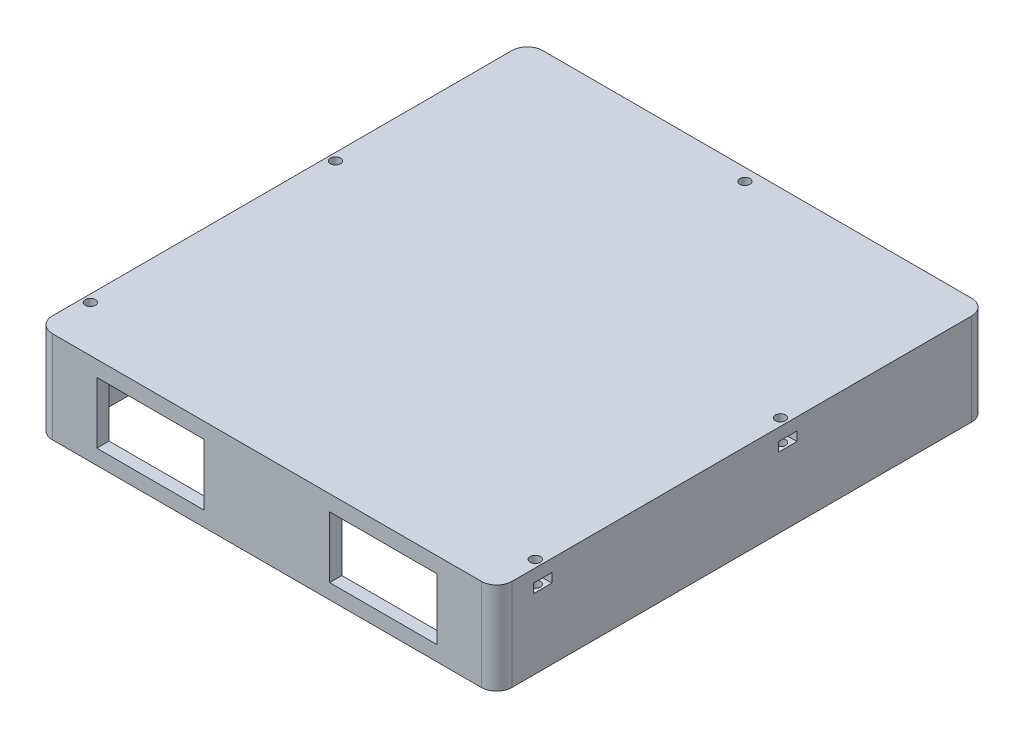
SolidWorks part; units mm, degrees
ref_plane "前视基准面" through (0, 0, 0) normal (0, 0, 1) x (1, 0, 0)
ref_plane "上视基准面" through (0, 0, 0) normal (0, 1, 0) x (1, 0, 0)
ref_plane "右视基准面" through (0, 0, 0) normal (1, 0, 0) x (0, 0, -1)
sketch "草图1" plane through (0, 0, 0) normal (0, 1, 0) x (1, 0, 0)
  line L1 (-75, 80) -> (75, 80)
  line L2 (-75, 80) -> (-75, -80)
  line L3 (-75, -80) -> (75, -80)
  line L4 (75, 80) -> (75, -80)
  line L5 (-75, 80) -> (75, -80) construction
  line L6 (-75, -80) -> (75, 80) construction
  point P0 (0, 0)
  dimension "D1" = 150
  dimension "D2" = 160
extrude "凸台-拉伸1" add sketch "草图1" along normal blind 30
fillet "圆角1" radius 5 4 edges at (75, 15, -80) (-75, 15, -80) (75, 15, 80) (-75, 15, 80)
sketch "草图3" plane through (0, 0, 0) normal (0, -1, 0) x (1, 0, 0)
  line L0 (-70, 80) -> (70, 80) construction
  line L1 (70, 76) -> (-70, 76)
  line L2 (70, 76) -> (70, -76)
  line L3 (70, -76) -> (-70, -76)
  line L4 (-70, 76) -> (-70, -76)
  line L5 (70, 76) -> (-70, -76) construction
  line L6 (70, -76) -> (-70, 76) construction
  line L7 (75, 75) -> (75, -75) construction
  point P0 (0, 0)
  dimension "D1" = 4
  dimension "D2" = 5
extrude "切除-拉伸2" cut sketch "草图3" against normal blind 26
sketch "草图9" plane through (-75, 0, 0) normal (-1, 0, 0) x (0, 0, 1)
  line L0 (80, 30) -> (80, 0) construction
  line L1 (68, 23) -> (62, 23)
  line L2 (68, 23) -> (68, 26)
  line L3 (68, 26) -> (62, 26)
  line L4 (62, 23) -> (62, 26)
  line L5 (68, 23) -> (62, 26) construction
  line L6 (68, 26) -> (62, 23) construction
  line L7 (-75, 30) -> (75, 30) construction
  line L8 (-12, 23) -> (-18, 23)
  line L9 (-12, 23) -> (-12, 26)
  line L10 (-12, 26) -> (-18, 26)
  line L11 (-18, 23) -> (-18, 26)
  line L12 (-12, 23) -> (-18, 26) construction
  line L13 (-12, 26) -> (-18, 23) construction
  point P0 (65, 24.5)
  point P9 (-15, 24.5)
  dimension "D1" = 15
  dimension "D2" = 6
  dimension "D3" = 3
  dimension "D4" = 4
  dimension "D5" = 6
  dimension "D6" = 3
  dimension "D7" = 80
  dimension "D8" = 4
extrude "切除-拉伸7" cut sketch "草图9" against normal through all
fillet "圆角2" radius 2 4 edges at (70, 13, 76) (70, 13, -76) (-70, 13, -76) (-70, 13, 76)
sketch "草图11" plane through (0, 30, 0) normal (0, 1, 0) x (1, 0, 0)
  line L0 (70, 80) -> (-70, 80) construction
  circle A0 centre (0, 76) radius 1.65
  dimension "D1" = 3.3
  dimension "D2" = 4
extrude "切除-拉伸8" cut sketch "草图11" against normal blind 8
sketch "草图12" plane through (0, 0, -80) normal (0, 0, -1) x (-1, 0, 0)
  line L0 (0, 0) -> (0, 95.539) construction
  line L1 (-70, 30) -> (70, 30) construction
  line L2 (3.25, 21.7) -> (-3.25, 21.7)
  line L3 (3.25, 21.7) -> (3.25, 25)
  line L4 (3.25, 25) -> (-3.25, 25)
  line L5 (-3.25, 21.7) -> (-3.25, 25)
  line L6 (3.25, 21.7) -> (-3.25, 25) construction
  line L7 (3.25, 25) -> (-3.25, 21.7) construction
  point P3 (0, 23.35)
  dimension "D2" = 3.3
  dimension "D1" = 6.5
  dimension "D3" = 5
extrude "切除-拉伸9" cut sketch "草图12" against normal blind 15
sketch "草图16" plane through (0, 0, 80) normal (0, 0, 1) x (1, 0, 0)
  line L0 (0, -31.9321) -> (0, 0) construction
  line L1 (0, 0) -> (0, 78.1937) construction
  line L2 (-55.4951, 24.8818) -> (-20.4951, 4.8818) construction
  line L5 (55.4951, 4.8818) -> (20.4951, 4.8818)
  line L10 (55.4951, 4.8818) -> (55.4951, 24.8818)
  line L11 (55.4951, 24.8818) -> (20.4951, 24.8818)
  line L12 (20.4951, 4.8818) -> (20.4951, 24.8818)
  line L17 (55.4951, 4.8818) -> (20.4951, 24.8818) construction
  line L18 (55.4951, 24.8818) -> (20.4951, 4.8818) construction
  line L19 (-55.4951, 4.8818) -> (-20.4951, 24.8818) construction
  line L20 (-20.4951, 4.8818) -> (-20.4951, 24.8818)
  line L21 (-55.4951, 24.8818) -> (-20.4951, 24.8818)
  line L22 (-55.4951, 4.8818) -> (-55.4951, 24.8818)
  line L23 (-55.4951, 4.8818) -> (-20.4951, 4.8818)
  point P4 (37.9951, 14.8818)
  point P9 (37.9951, 14.8818)
  point P14 (-37.9951, 14.8818)
  dimension "D1" = 35
  dimension "D2" = 20
extrude "切除-拉伸12" cut sketch "草图16" against normal blind 40
sketch "草图17" plane through (0, 30, 0) normal (0, 1, 0) x (1, 0, 0)
  line L0 (75, -62) -> (70, -62) construction
  line L2 (-75, 75) -> (-75, -75) construction
  line L3 (0, 0) -> (0, -177.4005) construction
  line L4 (75, 18) -> (70, 18) construction
  circle A0 centre (-72.6, -65) radius 1.65
  circle A1 centre (72.6, -65) radius 1.65
  circle A2 centre (-72.6, 15) radius 1.65
  circle A3 centre (72.6, 15) radius 1.65
  dimension "D2" = 2.4
  dimension "D3" = 3.3
  dimension "D4" = 3.3
  dimension "D5" = 3
  dimension "D6" = 2.4
  dimension "D1" = 3
extrude "切除-拉伸13" cut sketch "草图17" against normal blind 10
